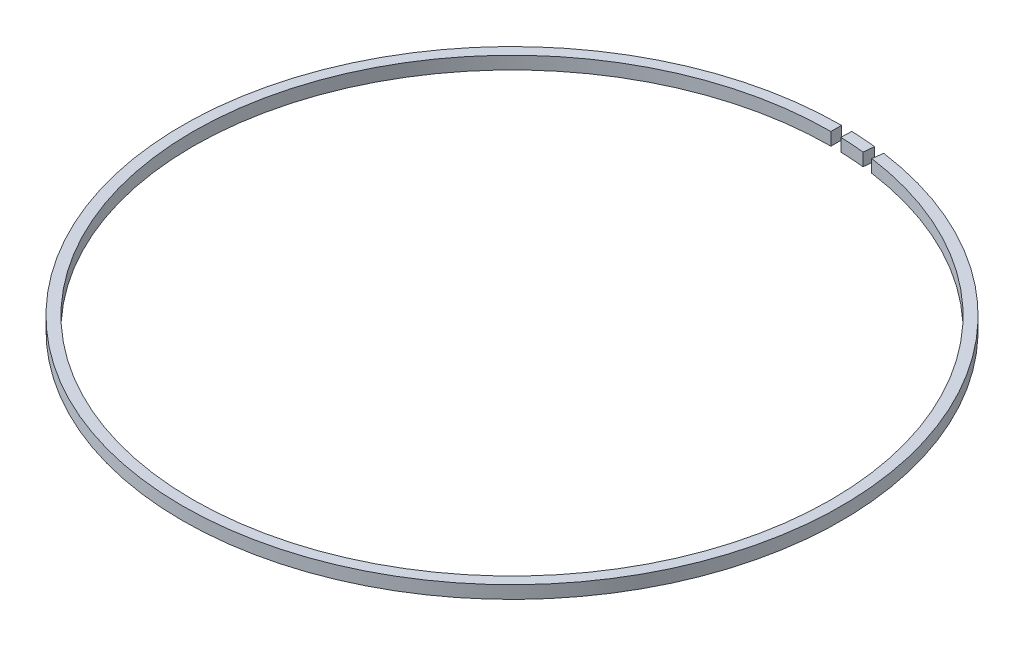
SolidWorks part; units mm, degrees
ref_plane "Front Plane" through (0, 0, 0) normal (0, 0, 1) x (1, 0, 0)
ref_plane "Top Plane" through (0, 0, 0) normal (0, 1, 0) x (1, 0, 0)
ref_plane "Right Plane" through (0, 0, 0) normal (1, 0, 0) x (0, 0, -1)
sketch "Sketch1" plane through (0, 0, 0) normal (0, 1, 0) x (1, 0, 0)
  circle A2 centre (0, 0) radius 77.5
  circle A3 centre (0, 0) radius 75
  dimension "D1" = 155
  dimension "D2" = 150
extrude "Boss-Extrude1" add sketch "Sketch1" along normal blind 3
sketch "Sketch2" plane through (0, 3, 0) normal (0, 1, 0) x (1, 0, 0)
  line L0 (0, 75) -> (0, 77.5)
  line L1 (2.4294, 77.4619) -> (2.3511, 74.9631)
  line L2 (7.9619, 74.5762) -> (8.2273, 77.0621)
  line L3 (10.6483, 76.765) -> (10.3048, 74.2887)
  circle A0 centre (0, 0) radius 75 construction
  circle A1 centre (0, 0) radius 77.5 construction
  arc A2 (2.4294, 77.4619) -> (0, 77.5) centre (0, 0) ccw
  arc A5 (2.3511, 74.9631) -> (0, 75) centre (0, 0) ccw
  arc A6 (10.6483, 76.765) -> (8.2273, 77.0621) centre (0.0013, 0.0107) ccw
  arc A7 (10.3048, 74.2887) -> (7.9619, 74.5762) centre (0.0013, 0.0107) ccw
  point P2 (25.6235, 67.1119)
  point P7 (0, 0)
  point P10 (15.8675, 73.3023)
  point P11 (0, 0)
  point P12 (30.9698, 66.8945)
  point P13 (29.447, 68.9774)
  point P14 (-0.2824, 74.9995)
  point P15 (5.238, 77.3228)
  point P16 (1.3847, 77.5)
  point P22 (0, 0)
  point P23 (0, 0)
  point P24 (8.73, 77.0067)
  point P25 (6.1112, 74.5341)
  point P26 (0, 0)
  point P27 (0, 0)
  point P28 (0, 0)
  point P29 (0, 0)
  point P30 (4.6591, 77.3598)
  point P31 (4.6591, 74.9872)
  point P32 (3.1945, 77.4341)
  point P33 (10.0911, 76.8402)
  point P34 (6.2113, 77.2507)
  point P35 (2.4238, 77.4868)
  point P36 (3.9862, 77.4595)
  point P37 (9.0695, 76.9675)
  point P38 (8.7615, 77.0032)
  point P39 (7.4163, 77.1443)
  point P40 (2.3511, 77.5)
  point P41 (10.059, 76.8444)
  point P42 (8.2273, 77.0621)
  point P43 (10.6483, 76.765)
extrude "Cut-Extrude1" cut sketch "Sketch2" against normal through all both and the other way through all
